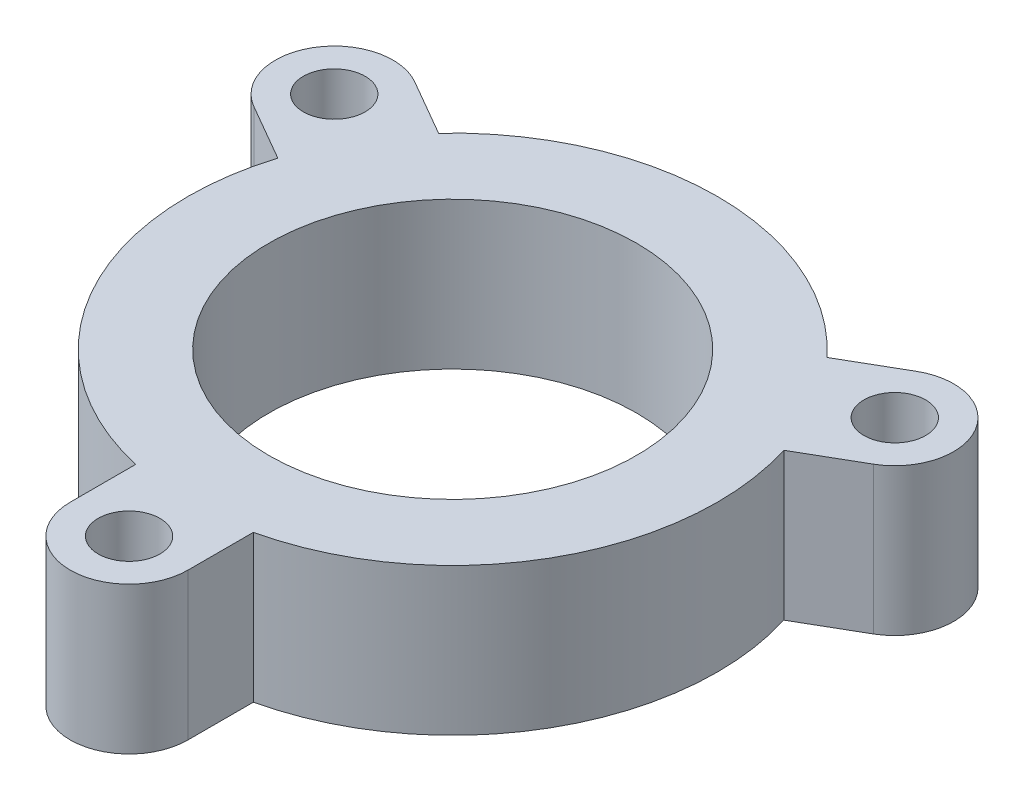
SolidWorks part; units mm, degrees
ref_plane "Front Plane" through (0, 0, 0) normal (0, 0, 1) x (1, 0, 0)
ref_plane "Top Plane" through (0, 0, 0) normal (0, 1, 0) x (1, 0, 0)
ref_plane "Right Plane" through (0, 0, 0) normal (1, 0, 0) x (0, 0, -1)
sketch "Sketch1" plane through (0, 0, 0) normal (0, 1, 0) x (1, 0, 0)
  line L0 (4, -22) -> (4, -17.5499)
  line L1 (-4, -22) -> (-4, -17.5499)
  line L2 (-21.0526, 7.5359) -> (-17.1987, 5.3109)
  line L3 (-17.0526, 14.4641) -> (-13.1987, 12.2391)
  line L4 (17.0526, 14.4641) -> (13.1987, 12.2391)
  line L5 (21.0526, 7.5359) -> (17.1987, 5.3109)
  circle A0 centre (0, 0) radius 18
  circle A1 centre (0, 0) radius 12.5
  circle A2 centre (0, -22) radius 2.1
  circle A3 centre (0, -22) radius 4
  circle A4 centre (-19.0526, 11) radius 4
  circle A5 centre (-19.0526, 11) radius 2.1
  circle A6 centre (19.0526, 11) radius 4
  circle A7 centre (19.0526, 11) radius 2.1
  point P28 (0, 0)
  dimension "D1" = 36
  dimension "D2" = 25
  dimension "D3" = 4.2
  dimension "D4" = 8
  dimension "D5" = 22
  dimension "D6" = 3
extrude "Boss-Extrude1" add sketch "Sketch1" along normal blind 10 contours A0 A1 | A6 A7 | A6 A0 L5 | A6 L4 A0 | A4 A0 L3 | A4 A5 | A4 L2 A0 | A3 A2 | A3 L0 A0 | A3 A0 L1
